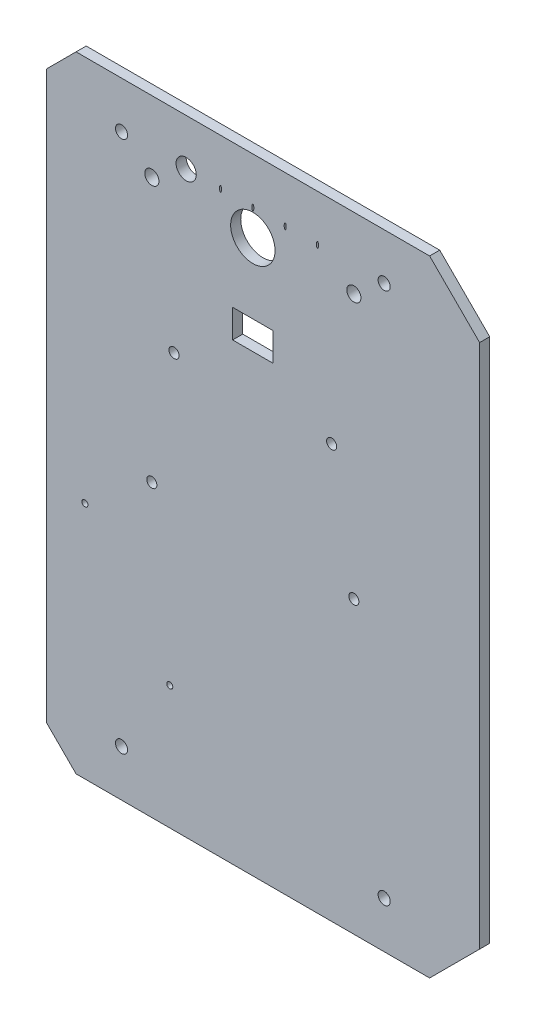
SolidWorks part; units mm, degrees
material "Alliage 1060"
ref_plane "Plan de dessus" through (0, 0, 0) normal (0, 0, 1) x (1, 0, 0)
ref_plane "Plan de droite" through (0, 0, 0) normal (0, 1, 0) x (1, 0, 0)
ref_plane "Plan de face" through (0, 0, 0) normal (1, 0, 0) x (0, 0, -1)
sketch "Esquisse1" plane through (0, 0, 0) normal (0, 0, 1) x (1, 0, 0)
  line L0 (0, 0) -> (-175, 0)
  line L1 (-175, 0) -> (-199.7487, 24.7487)
  line L2 (-199.7487, 24.7487) -> (-199.7487, 284.7487)
  line L3 (-199.7487, 284.7487) -> (-175, 309.4975)
  line L4 (-175, 309.4975) -> (0, 309.4975)
  line L5 (0, 309.4975) -> (24.7487, 284.7487)
  line L6 (24.7487, 284.7487) -> (24.7487, 24.7487)
  line L7 (24.7487, 24.7487) -> (0, 0)
  dimension "D1" = 260
  dimension "D2" = 35
  dimension "D3" = 135
  dimension "D4" = 175
extrude "Base" add sketch "Esquisse1" along normal blind 5
sketch "Esquisse2" plane through (0, 0, 5) normal (0, 0, 1) x (1, 0, 0)
  line L0 (-199.7487, 284.7487) -> (-199.7487, 24.7487) construction
  line L1 (-175, 0) -> (0, 0) construction
  line L2 (-199.7487, 154.7487) -> (24.7487, 154.7487) construction
  line L3 (24.7487, 24.7487) -> (24.7487, 284.7487) construction
  line L4 (-87.5, 309.4975) -> (-87.5, 0) construction
  line L5 (0, 309.4975) -> (-175, 309.4975) construction
  line L7 (-132.5, 199.7487) -> (-42.5, 199.7487) construction
  line L8 (-132.5, 199.7487) -> (-132.5, 109.7487) construction
  line L9 (-132.5, 109.7487) -> (-42.5, 109.7487) construction
  line L10 (-42.5, 199.7487) -> (-42.5, 109.7487) construction
  circle A0 centre (-152.4987, 23) radius 3
  circle A1 centre (-152.4987, 286.4975) radius 3
  circle A2 centre (-22.5013, 23) radius 3
  circle A3 centre (-22.5013, 286.4975) radius 3
  circle A4 centre (-137.5, 143.7487) radius 2.5
  circle A5 centre (-126.5, 204.7487) radius 2.5
  circle A6 centre (-37.5, 143.7487) radius 2.5
  circle A7 centre (-48.5, 204.7487) radius 2.5
  point P25 (-87.5, 199.7487)
  point P26 (-132.5, 154.7487)
  dimension "D1" = 6
  dimension "D6" = 5
  dimension "D8" = 5
  dimension "D2" = 47.25
  dimension "D3" = 23
  dimension "D4" = 90
  dimension "D5" = 34
  dimension "D7" = 5
  dimension "D9" = 5
  dimension "D10" = 6
  dimension "D11" = 90
sketch "Esquisse4" plane through (0, 0, 5) normal (0, 0, 1) x (1, 0, 0)
  line L0 (-87.5, 309.4975) -> (-87.5, 0) construction
  line L1 (0, 309.4975) -> (-175, 309.4975) construction
  line L2 (-132.5, 199.7487) -> (-42.5, 199.7487) construction
  line L3 (-97.5, 238.7487) -> (-77.5, 238.7487)
  line L4 (-97.5, 238.7487) -> (-97.5, 224.7487)
  line L5 (-97.5, 224.7487) -> (-77.5, 224.7487)
  line L6 (-77.5, 238.7487) -> (-77.5, 224.7487)
  line L7 (-87.5, 273.4975) -> (-37.5, 273.4975) construction
  line L8 (-87.5, 273.4975) -> (-137.5, 273.4975) construction
  line L9 (24.7487, 24.7487) -> (24.7487, 284.7487) construction
  circle A0 centre (-87.5, 273.4975) radius 11
  circle A1 centre (-137.5, 274.4975) radius 3.5
  circle A2 centre (-37.5, 274.4975) radius 3.5
  ellipse E0 centre (-103.5, 286.4975) end of major axis (-103.5, 284.9975) minor radius 0.5
  ellipse E5 centre (-87.5, 286.4975) end of major axis (-87.5, 284.9975) minor radius 0.5
  ellipse E6 centre (-71.5, 286.4975) end of major axis (-71.5, 284.9975) minor radius 0.5
  ellipse E7 centre (-55.5, 286.4975) end of major axis (-55.5, 284.9975) minor radius 0.5
  point P28 (-87.5, 238.7487)
  dimension "D4" = 22
  dimension "D7" = 7
  dimension "D1" = 3
  dimension "D2" = 1
  dimension "D3" = 16
  dimension "D5" = 36
  dimension "D8" = 35
  dimension "D10" = 25
  dimension "D11" = 14
  dimension "D12" = 20
  dimension "D13" = 100
  dimension "D14" = 37.5
  dimension "D6" = 4
  dimension "D9" = 2
sketch "Esquisse8" plane through (0, 0, 5) normal (0, 0, 1) x (1, 0, 0)
  circle A1 centre (-120.5, 286.4975) radius 5
  dimension "D3" = 10
  dimension "D4" = 17
extrude "Enlèv. mat.-Extru.7" cut sketch "Esquisse8" against normal blind 10
extrude "Enlèv. mat.-Extru.8" cut sketch "Esquisse4" against normal blind 10
extrude "Enlèv. mat.-Extru.9" cut sketch "Esquisse2" against normal blind 10
sketch "logo DVB" plane through (0, 0, 0) normal (0, 0, -1) x (-1, 0, 0)
  line L0 (87.5, 0) -> (87.5, 25) construction
  line L1 (175, 0) -> (0, 0) construction
sketch "Esquisse11" plane through (0, 0, 5) normal (0, 0, 1) x (1, 0, 0)
  line L0 (-170.6149, 118.1524) -> (-170.6149, 61.1524) construction
  line L1 (-170.6149, 61.1524) -> (-170.6149, 0) construction
  line L7 (-170.6149, 61.1524) -> (-128.6149, 61.1524) construction
  line L8 (-87.5, 309.4975) -> (-87.5, -98.2433) construction
  line L9 (0, 309.4975) -> (-175, 309.4975) construction
  line L10 (-189.7487, -12.261) -> (-189.7487, 134.7487)
  line L11 (-199.7487, -12.261) -> (-189.7487, -12.261)
  line L12 (-199.7487, 326.5238) -> (-199.7487, -12.261)
  line L13 (-189.7487, 326.5238) -> (-199.7487, 326.5238)
  line L14 (-189.7487, 134.7487) -> (-189.7487, 326.5238)
  line L15 (-175, 0) -> (0, 0) construction
  line L16 (-170.6149, 61.1524) -> (-199.7487, 61.1524) construction
  circle A0 centre (-170.6149, 118.1524) radius 1.5
  circle A1 centre (-128.6149, 61.1524) radius 1.5
  dimension "D3" = 3
  dimension "D1" = 42
  dimension "D2" = 57
  dimension "D4" = 61.1524
  dimension "D5" = 29.1338
extrude "Enlèv. mat.-Extru.11" cut sketch "Esquisse11" against normal blind 5
